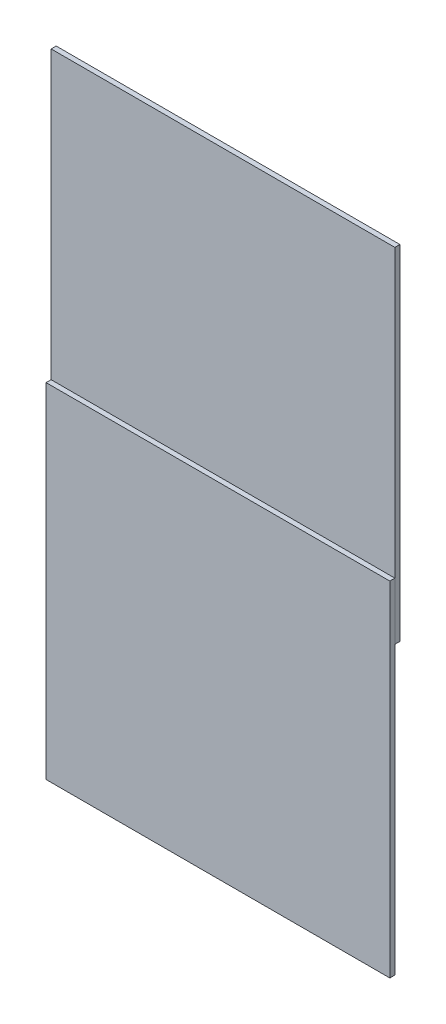
SolidWorks part; units mm, degrees
ref_plane "Ebene vorne" through (0, 0, 0) normal (0, 0, 1) x (1, 0, 0)
ref_plane "Ebene oben" through (0, 0, 0) normal (0, 1, 0) x (1, 0, 0)
ref_plane "Ebene rechts" through (0, 0, 0) normal (1, 0, 0) x (0, 0, -1)
sketch "Skizze2" plane through (0, 0, 0) normal (0, 0, 1) x (1, 0, 0)
  line L1 (0, 0) -> (150, 0)
  line L2 (0, 0) -> (0, -150)
  line L3 (0, -150) -> (150, -150)
  line L4 (150, 0) -> (150, -150)
  dimension "D1" = 150
  dimension "D2" = 150
extrude "Aufsatz-Linear austragen1" add sketch "Skizze2" along normal blind 2.2
sketch "Skizze3" plane through (0, 0, 0) normal (0, 0, -1) x (-1, 0, 0)
  line L0 (0, 0) -> (0, -150) construction
  line L1 (0, -25) -> (-150, -25)
  line L2 (0, -25) -> (0, 125)
  line L3 (0, 125) -> (-150, 125)
  line L4 (-150, -25) -> (-150, 125)
  line L5 (-150, 0) -> (0, 0) construction
  dimension "D1" = 150
  dimension "D2" = 25
extrude "Aufsatz-Linear austragen3" add sketch "Skizze3" along normal blind 2.2 separate body
sketch "Skizze4" plane through (0, 0, -2.2) normal (0, 0, -1) x (-1, 0, 0)
  line L0 (-150, -25) -> (0, -25) construction
  line L2 (-65.9972, -25) -> (-64.9972, -25)
  line L3 (-65.9972, -25) -> (-65.9972, 0)
  line L4 (-65.9972, 0) -> (-64.9972, 0)
  line L5 (-64.9972, -25) -> (-64.9972, 0)
  dimension "D1" = 1
  dimension "D2" = 25
extrude "Aufsatz-Linear austragen4" add sketch "Skizze4" along normal blind 1
